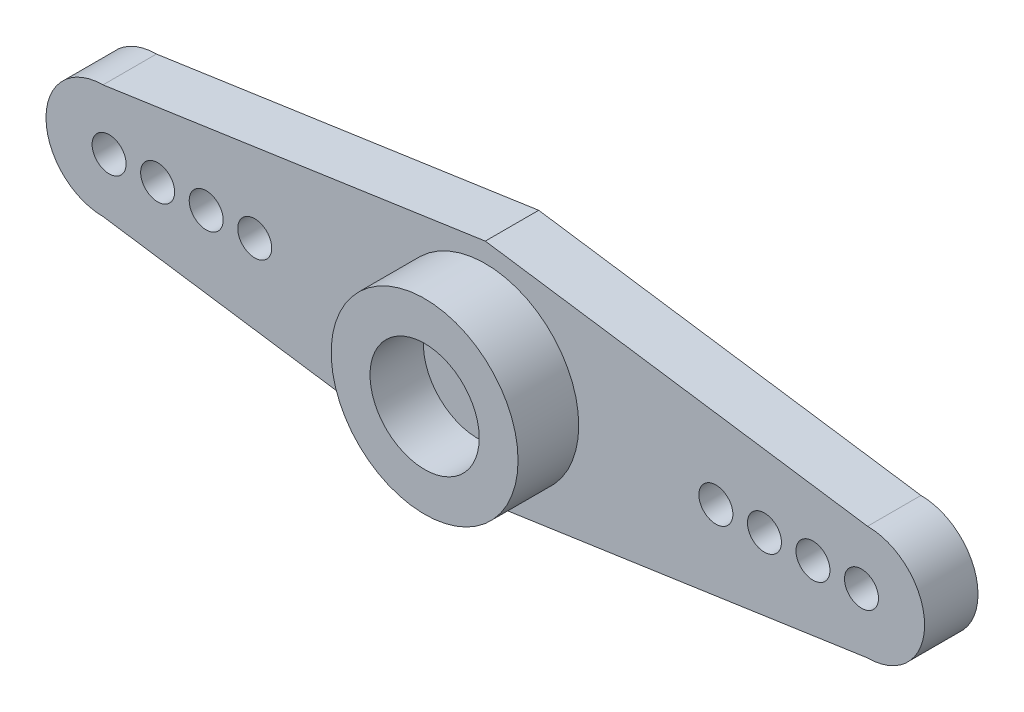
SolidWorks part; units mm, degrees
material "Nylon 6/10"
ref_plane "Front Plane" through (0, 0, 0) normal (0, 0, 1) x (1, 0, 0)
ref_plane "Top Plane" through (0, 0, 0) normal (0, 1, 0) x (1, 0, 0)
ref_plane "Right Plane" through (0, 0, 0) normal (1, 0, 0) x (0, 0, -1)
sketch "Sketch1" plane through (0, 0, 0) normal (0, 0, 1) x (1, 0, 0)
  line L1 (-22.987, -5.9055) -> (22.987, -5.9055)
  line L2 (-22.987, -5.9055) -> (-22.987, 5.9055)
  line L3 (-22.987, 5.9055) -> (22.987, 5.9055)
  line L4 (22.987, -5.9055) -> (22.987, 5.9055)
  line L5 (-22.987, -5.9055) -> (22.987, 5.9055) construction
  line L6 (-22.987, 5.9055) -> (22.987, -5.9055) construction
  point P0 (0, 0)
extrude "Extrude1" add sketch "Sketch1" along normal blind 5.969
sketch "Sketch2" plane through (0, 0, 5.969) normal (0, 0, 1) x (1, 0, 0)
  circle A0 centre (0, 0) radius 4.8895
extrude "Extrude2" cut sketch "Sketch2" against normal blind 3.175 flip side to cut
sketch "Sketch3" plane through (0, 0, 5.969) normal (0, 0, 1) x (1, 0, 0)
  circle A0 centre (0, 0) radius 2.8575
extrude "Extrude3" cut sketch "Sketch3" against normal blind 2.794
sketch "Sketch4" plane through (0, 0, 0) normal (0, 0, -1) x (-1, 0, 0)
  line L0 (0, 0) -> (-12.065, 0) construction
hole_wizard "#50 (0.07) Diameter Hole1" positions "3DSketch1" profile "Sketch5" hole size "#50" standard "Ansi Inch"
sketch3d "3DSketch1"
  point P0 (12.065, 0, 0)
sketch "Sketch5" plane through (12.065, 0, 0) normal (1, 0, 0) x (0, 1, 0)
  line L0 (0, 0) -> (0, 5.6142)
  line L1 (0, 5.6142) -> (0.889, 5.08)
  line L2 (0.889, 5.08) -> (0.889, 0)
  line L5 (0.889, 0) -> (0, 0)
  line L10 (0, 5.6142) -> (-0.889, 5.08) construction
  line L11 (0, -6.35) -> (0, 107.95) construction
  dimension "Hole Dia." = 1.778
  dimension "Hole Depth" = 5.08
  dimension "Drill Angle" = 118
pattern_linear "LPattern1" count 4 spacing 2.54 along (1, 0, 0) of "#50 (0.07) Diameter Hole1"
mirror "Mirror1" about plane through (0, 0, 0) normal (1, 0, 0) of "LPattern1", "#50 (0.07) Diameter Hole1"
sketch "Sketch6" plane through (0, 0, 0) normal (0, 0, -1) x (-1, 0, 0)
  line L0 (22.987, 0) -> (20.0025, 0) construction
  line L1 (22.987, 5.9055) -> (22.987, -5.9055) construction
  line L2 (20.0025, -2.9845) -> (0, -5.9055)
  line L3 (22.987, -5.9055) -> (-22.987, -5.9055) construction
  line L4 (20.0025, 2.9845) -> (0, 5.9055)
  line L5 (-22.987, 5.9055) -> (22.987, 5.9055) construction
  arc A0 (22.987, 0) -> (20.0025, -2.9845) centre (20.0025, 0) cw
  arc A1 (22.987, 0) -> (20.0025, 2.9845) centre (20.0025, 0) ccw
extrude "Extrude4" cut sketch "Sketch6" against normal through all flip side to cut
mirror "Mirror2" about plane through (0, 0, 0) normal (1, 0, 0) of "Extrude4"
